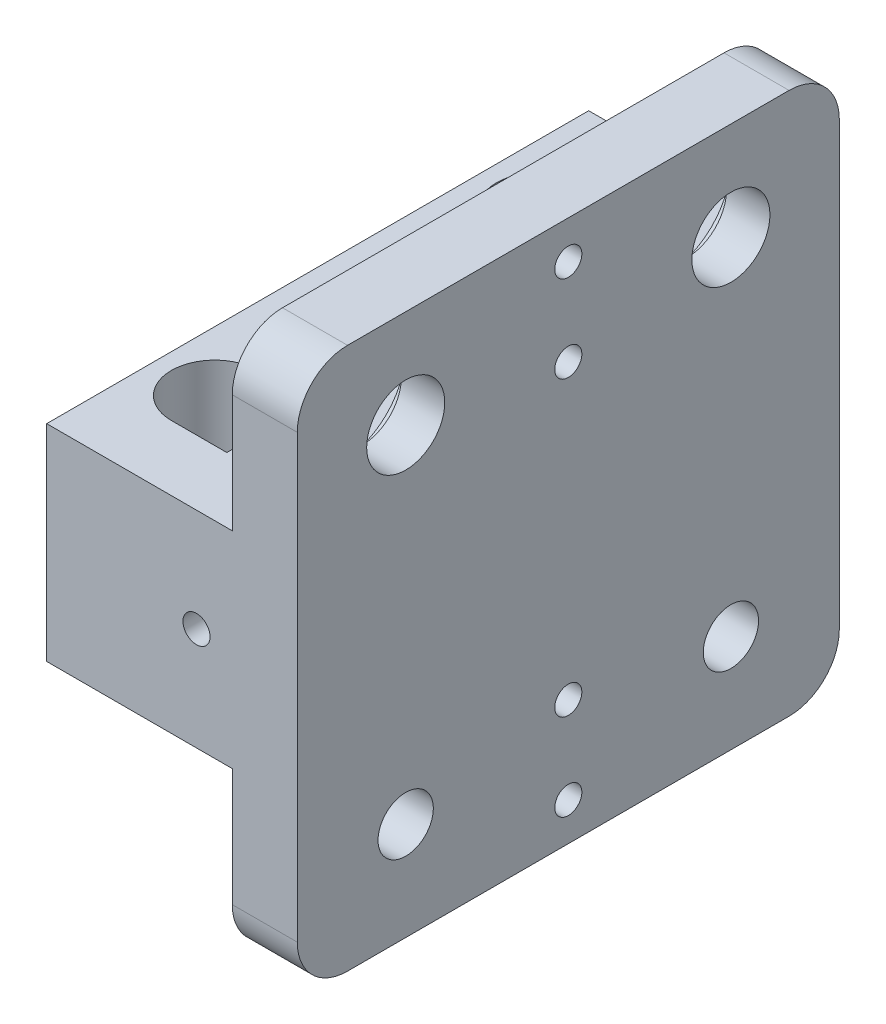
SolidWorks part; units mm, degrees
ref_plane "Front" through (0, 0, 0) normal (0, 0, 1) x (1, 0, 0)
ref_plane "Top" through (0, 0, 0) normal (0, 1, 0) x (1, 0, 0)
ref_plane "Right" through (0, 0, 0) normal (1, 0, 0) x (0, 0, -1)
sketch "Sketch2" plane through (0, 0, 0) normal (1, 0, 0) x (0, 0, -1)
  line L1 (-25, -25) -> (25, -25)
  line L2 (-25, -25) -> (-25, 25)
  line L3 (-25, 25) -> (25, 25)
  line L4 (25, -25) -> (25, 25)
  line L5 (0, 25) -> (0, -25) construction
  line L6 (-25, 0) -> (25, 0) construction
  point P0 (0, 0)
  dimension "D1" = 50
  dimension "D2" = 50
extrude "Boss-Extrude1" add sketch "Sketch2" along normal blind 6
sketch "Sketch3" plane through (25, 0, 0) normal (0, 1, 0) x (0, 0, 1)
  line L0 (-25, -19) -> (-25, -25) construction
  line L2 (25, -25) -> (-25, -25) construction
  line L3 (-25, -44.1188) -> (25, -44.1188)
  line L4 (-25, -44.1188) -> (-25, -25)
  line L5 (-19, -32.4282) -> (-19, -36.6188)
  line L6 (-25, -25) -> (25, -25)
  line L7 (25, -44.1188) -> (25, -25)
  line L8 (-15, -34.7376) -> (-11, -32.4282) construction
  line L9 (-11, -32.4282) -> (-11, -27.8094)
  line L10 (-11, -27.8094) -> (-15, -25.5)
  line L11 (-15, -25.5) -> (-19, -27.8094)
  line L12 (-19, -27.8094) -> (-19, -32.4282)
  line L13 (-19, -32.4282) -> (-15, -34.7376) construction
  line L14 (-11, -36.6188) -> (-11, -32.4282)
  line L15 (-15, -30.1188) -> (15, -30.1188) construction
  line L16 (19, -32.4282) -> (15, -34.7376) construction
  line L17 (15, -34.7376) -> (11, -32.4282) construction
  line L18 (11, -36.6188) -> (11, -32.4282)
  line L19 (19, -27.8094) -> (19, -32.4282)
  line L20 (15, -25.5) -> (19, -27.8094)
  line L21 (11, -27.8094) -> (15, -25.5)
  line L22 (11, -32.4282) -> (11, -27.8094)
  line L23 (19, -32.4282) -> (19, -36.6188)
  line L27 (0, -25) -> (0, -30.1188) construction
  circle A0 centre (-15, -30.1188) radius 4 construction
  arc A1 (-19, -36.6188) -> (-11, -36.6188) centre (-15, -36.6188) ccw
  circle A2 centre (15, -30.1188) radius 4 construction
  arc A3 (19, -36.6188) -> (11, -36.6188) centre (15, -36.6188) cw
  dimension "D1" = 30
  dimension "D2" = 3.5
  dimension "D4" = 8
  dimension "D3" = 0.5
  dimension "D5" = 6.5
extrude "Boss-Extrude2" add sketch "Sketch3" against normal mid plane 19
sketch "Sketch5" plane through (9.5, 9.5, 0) normal (0, -1, 0) x (0, 0, 1)
  line L0 (-19, 16) -> (-11, 16)
  line L1 (11, 16) -> (19, 16)
  line L4 (-11, 12.3094) -> (-11, 21.1188)
  line L5 (-15, 10) -> (-11, 12.3094)
  line L6 (-19, 12.3094) -> (-15, 10)
  line L7 (-19, 21.1188) -> (-19, 12.3094)
  line L8 (-11, 12.3094) -> (-11, 16)
  line L9 (-15, 10) -> (-11, 12.3094)
  line L10 (-19, 12.3094) -> (-15, 10)
  line L11 (-19, 16) -> (-19, 12.3094)
  line L12 (19, 12.3094) -> (19, 21.1188)
  line L13 (15, 10) -> (19, 12.3094)
  line L14 (11, 12.3094) -> (15, 10)
  line L15 (11, 21.1188) -> (11, 12.3094)
  line L16 (19, 12.3094) -> (19, 16)
  line L17 (15, 10) -> (19, 12.3094)
  line L18 (11, 12.3094) -> (15, 10)
  line L19 (11, 16) -> (11, 12.3094)
  arc A1 (-11, 21.1188) -> (-19, 21.1188) centre (-15, 21.1188) ccw
  arc A3 (19, 21.1188) -> (11, 21.1188) centre (15, 21.1188) ccw
  dimension "D3" = 6
  dimension "D1" = 0
  dimension "D2" = 0
extrude "Boss-Extrude3" add sketch "Sketch5" along normal blind 12
sketch "Sketch6" plane through (0, 0, 0) normal (1, 0, 0) x (0, 0, -1)
  line L1 (15, -15.95) -> (-15, -15.95) construction
  line L2 (15, -15.95) -> (15, 15.95) construction
  line L3 (15, 15.95) -> (-15, 15.95) construction
  line L4 (-15, -15.95) -> (-15, 15.95) construction
  line L5 (0, 15.95) -> (0, -15.95) construction
  line L6 (15, 0) -> (-15, 0) construction
  circle A0 centre (-15, 15.95) radius 3.6
  circle A1 centre (15, 15.95) radius 3.6
  circle A2 centre (-15, -15.95) radius 2.55
  circle A3 centre (15, -15.95) radius 2.55
  point P0 (0, 0)
  dimension "D3" = 7.2
  dimension "D4" = 5.1
  dimension "D1" = 31.9
  dimension "D2" = 30
extrude "Cut-Extrude2" cut sketch "Sketch6" along normal through all
sketch "Sketch7" plane through (0, 0, 0) normal (-1, 0, 0) x (0, 0, 1)
  circle A0 centre (-15, -15.95) radius 5.05
  circle A1 centre (15, -15.95) radius 5.05
  circle A2 centre (-15, 15.95) radius 6
  circle A3 centre (15, 15.95) radius 6
  dimension "D1" = 12
  dimension "D2" = 10.1
extrude "Cut-Extrude3" cut sketch "Sketch7" against normal blind 2
hole_wizard "M4x0.7 Tapped Hole1" positions "Sketch9" profile "Sketch10" tap size "M4x0.7" standard "ANSI Metric"
sketch "Sketch9" plane through (-19.1188, 0, 0) normal (1, 0, 0) x (0, -1, 0)
  line L0 (5.5, -15) -> (5.5, 15) construction
  line L3 (5.5, 0) -> (0, 0) construction
  line L6 (9.5, 25) -> (9.5, -25) construction
  point P0 (5.5, 15)
  point P2 (5.5, -15)
  dimension "D1" = 30
  dimension "D2" = 4
sketch "Sketch10" plane through (-19.1188, -5.5, -15) normal (0, 1, 0) x (0, 0, 1)
  line L0 (0, 0) -> (0, 3.5)
  line L1 (0, 3.5) -> (1.65, 3.5)
  line L2 (1.65, 3.5) -> (1.65, 0)
  line L5 (1.65, 0) -> (0, 0)
  line L11 (0, -6.35) -> (0, 107.95) construction
  dimension "Thread Major Dia." = 3.3
  dimension "Thru Tap Drill Depth" = 3.5
hole_wizard "M4x0.7 Tapped Hole2" positions "Sketch11" profile "Sketch12" tap size "M4x0.7" standard "ANSI Metric"
sketch "Sketch11" plane through (-19.1188, 0, 0) normal (-1, 0, 0) x (0, 0, 1)
  line L0 (-9.525, 1.9682) -> (9.525, 1.9682) construction
  line L3 (0, 1.9682) -> (0, 0) construction
  point P0 (-9.525, 1.9682)
  point P2 (9.525, 1.9682)
  dimension "D1" = 19.05
  dimension "D2" = 1.9682
sketch "Sketch12" plane through (-19.1188, 1.9682, -9.525) normal (0, 1, 0) x (0, 0, 1)
  line L0 (0, 0) -> (0, 10.9914)
  line L1 (0, 10.9914) -> (1.65, 10)
  line L2 (1.65, 10) -> (1.65, 0)
  line L5 (1.65, 0) -> (0, 0)
  line L10 (0, 10.9914) -> (-1.65, 10) construction
  line L11 (0, -6.35) -> (0, 107.95) construction
  dimension "Tap Drill Dia." = 3.3
  dimension "Tap Drill Depth" = 10
  dimension "Drill Angle" = 118
cosmetic thread "Hole Thread1" parameters "D1"=8, "D2"=4
cosmetic thread "Hole Thread2" parameters "D1"=8, "D2"=4
fillet "Fillet1" radius 4.635 4 edges at (3, 25, 25) (3, 25, -25) (3, -25, -25) (3, -25, 25)
hole_wizard "M3x0.5 Tapped Hole1" positions "Sketch13" profile "Sketch14" tap size "M3x0.5" standard "ANSI Metric" end condition through all
sketch "Sketch13" plane through (0, 0, 0) normal (-1, 0, 0) x (0, 0, 1)
  line L0 (0, 21.5) -> (0, -21.5) construction
  line L2 (-20.365, 25) -> (20.365, 25) construction
  point P0 (0, 21.5)
  point P2 (0, -21.5)
  point P4 (0, -13.5)
  point P6 (0, 13.5)
  dimension "D1" = 8
  dimension "D2" = 8
  dimension "D3" = 3.5
sketch "Sketch14" plane through (0, 21.5, 0) normal (0, 1, 0) x (0, 0, 1)
  line L0 (0, 0) -> (0, 6)
  line L1 (0, 6) -> (1.25, 6)
  line L2 (1.25, 6) -> (1.25, 0)
  line L5 (1.25, 0) -> (0, 0)
  line L11 (0, -6.35) -> (0, 107.95) construction
  dimension "Thru Tap Drill Dia." = 2.5
  dimension "Thru Tap Drill Depth" = 6
cosmetic thread "Hole Thread3" parameters "D2"=3
cosmetic thread "Hole Thread4" parameters "D2"=3
cosmetic thread "Hole Thread5" parameters "D2"=3
cosmetic thread "Hole Thread6" parameters "D2"=3
hole_wizard "M4x0.7 Tapped Hole3" positions "Sketch15" profile "Sketch16" tap size "M4x0.7" standard "ANSI Metric"
sketch "Sketch15" plane through (0, 9.5, 0) normal (0, 1, 0) x (1, 0, 0)
  line L0 (0, -25) -> (0, 25) construction
  line L1 (-4.95, 0) -> (0, 0) construction
  point P0 (-4.95, 0)
  dimension "D1" = 4.95
sketch "Sketch16" plane through (-4.95, 9.5, 0) normal (1, 0, 0) x (0, 0, 1)
  line L0 (0, 0) -> (0, 6.9914)
  line L1 (0, 6.9914) -> (1.65, 6)
  line L2 (1.65, 6) -> (1.65, 0)
  line L5 (1.65, 0) -> (0, 0)
  line L10 (0, 6.9914) -> (-1.65, 6) construction
  line L11 (0, -6.35) -> (0, 107.95) construction
  dimension "Tap Drill Dia." = 3.3
  dimension "Tap Drill Depth" = 6
  dimension "Drill Angle" = 118
cosmetic thread "Hole Thread7" parameters "D1"=6, "D2"=4
sketch "Sketch17" plane through (0, 0, -25) normal (0, 0, -1) x (-1, 0, 0)
  line L0 (0, 9.5) -> (19.1188, 9.5) construction
  circle A0 centre (3.3, 0) radius 1.25
  dimension "D1" = 3.3
  dimension "D2" = 2.5
  dimension "D3" = 9.5
extrude "Cut-Extrude4" cut sketch "Sketch17" against normal through all
sketch "Sketch18" plane through (-19.1188, 0, 0) normal (-1, 0, 0) x (0, 0, 1)
  circle A0 centre (-9.525, 1.9682) radius 3
  circle A1 centre (9.525, 1.9682) radius 3
  dimension "D1" = 6
extrude "Cut-Extrude5" cut sketch "Sketch18" against normal blind 2 flip side to cut
